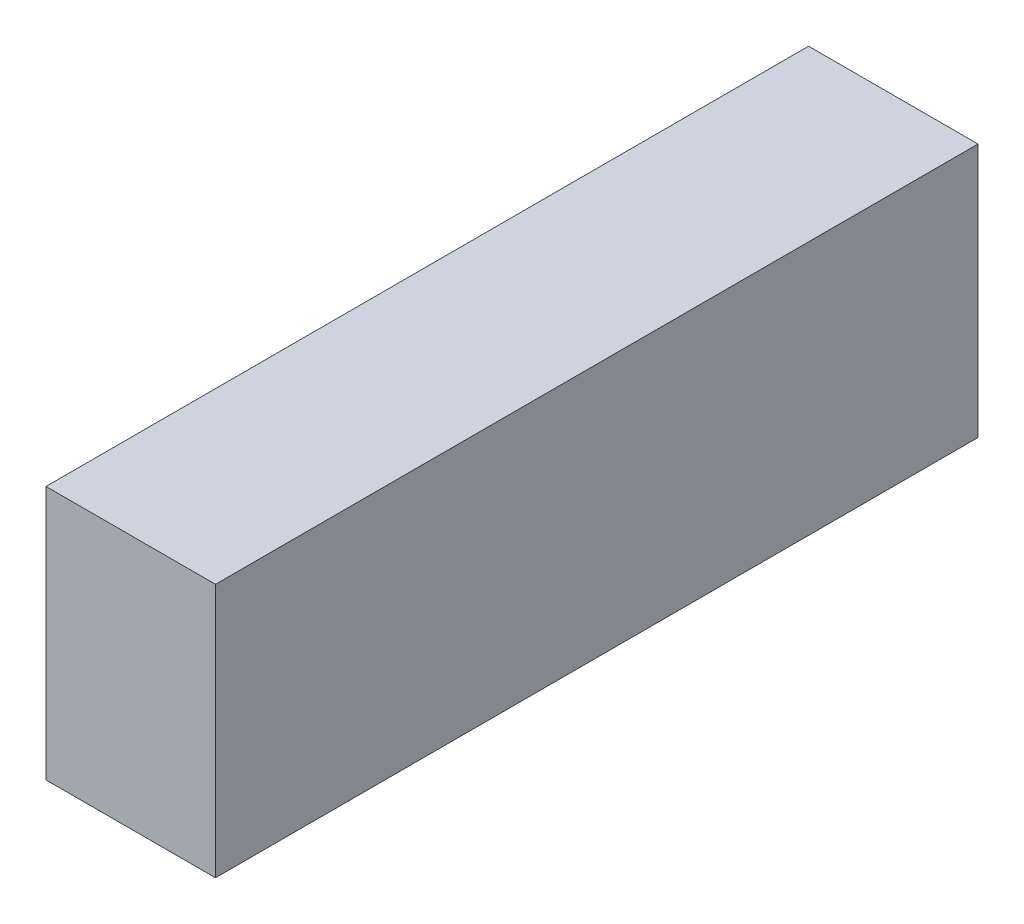
SolidWorks part; units mm, degrees
ref_plane "Front Plane" through (0, 0, 0) normal (0, 0, 1) x (1, 0, 0)
ref_plane "Top Plane" through (0, 0, 0) normal (0, 1, 0) x (1, 0, 0)
ref_plane "Right Plane" through (0, 0, 0) normal (1, 0, 0) x (0, 0, -1)
sketch "Sketch1" plane through (0, 0, 0) normal (0, 0, 1) x (1, 0, 0)
  line L1 (-4.2333, -6.35) -> (4.2333, -6.35)
  line L2 (-4.2333, -6.35) -> (-4.2333, 6.35)
  line L3 (-4.2333, 6.35) -> (4.2333, 6.35)
  line L4 (4.2333, -6.35) -> (4.2333, 6.35)
  line L5 (0, 6.35) -> (0, -6.35) construction
  line L6 (-4.2333, 0) -> (4.2333, 0) construction
  point P0 (0, 0)
  dimension "D1" = 8.4667
  dimension "D2" = 12.7
extrude "Boss-Extrude1" add sketch "Sketch1" along normal blind 38.1
